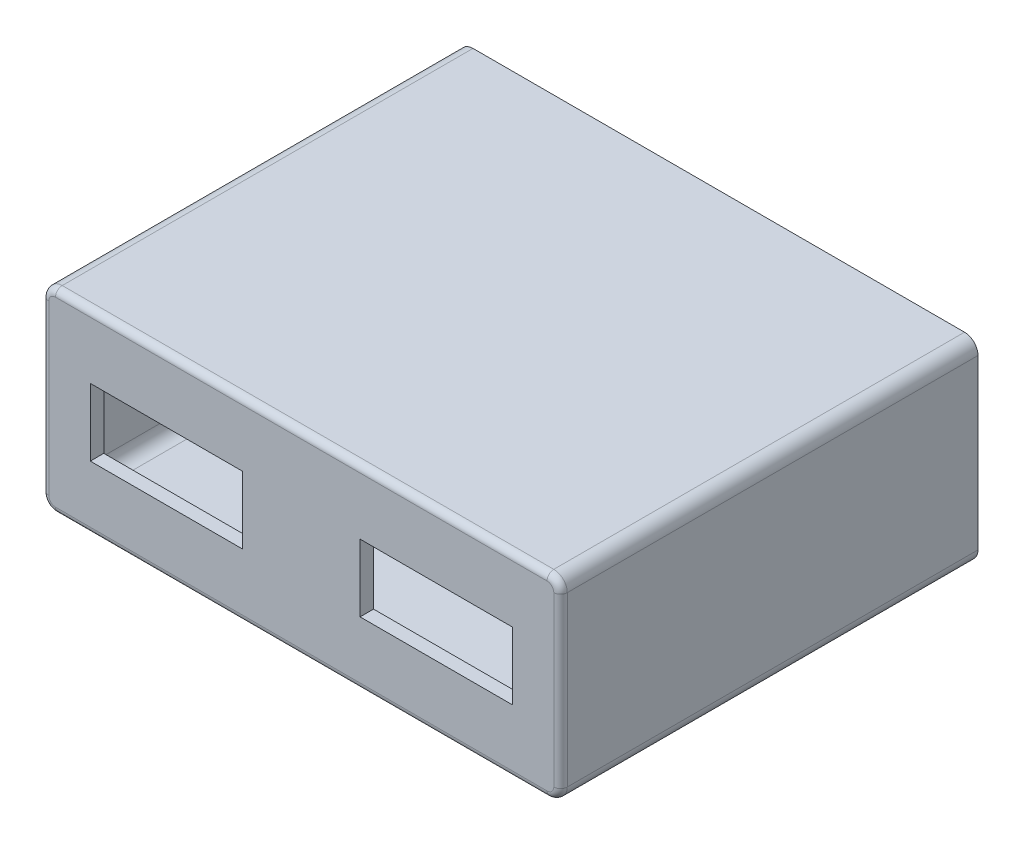
SolidWorks part; units mm, degrees
ref_plane "Front Plane" through (0, 0, 0) normal (0, 0, 1) x (1, 0, 0)
ref_plane "Top Plane" through (0, 0, 0) normal (0, 1, 0) x (1, 0, 0)
ref_plane "Right Plane" through (0, 0, 0) normal (1, 0, 0) x (0, 0, -1)
sketch "Sketch1" plane through (0, 0, 0) normal (0, 0, 1) x (1, 0, 0)
  line L1 (-34.5, -12.5) -> (34.5, -12.5)
  line L2 (-36.5, -10.5) -> (-36.5, 10.5)
  line L3 (-34.5, 12.5) -> (34.5, 12.5)
  line L4 (36.5, -10.5) -> (36.5, 10.5)
  line L5 (-36.5, -12.5) -> (36.5, 12.5) construction
  line L6 (-36.5, 12.5) -> (36.5, -12.5) construction
  line L9 (36.5, -14.5) -> (-36.5, -14.5)
  line L10 (38.5, -12.5) -> (38.5, 12.5)
  line L11 (36.5, 14.5) -> (-36.5, 14.5)
  line L12 (-38.5, -12.5) -> (-38.5, 12.5)
  line L13 (38.5, -14.5) -> (-38.5, 14.5) construction
  line L14 (38.5, 14.5) -> (-38.5, -14.5) construction
  arc A0 (-36.5, -14.5) -> (-38.5, -12.5) centre (-36.5, -12.5) cw
  arc A1 (-36.5, 14.5) -> (-38.5, 12.5) centre (-36.5, 12.5) ccw
  arc A2 (38.5, 12.5) -> (36.5, 14.5) centre (36.5, 12.5) ccw
  arc A3 (36.5, -14.5) -> (38.5, -12.5) centre (36.5, -12.5) ccw
  arc A4 (34.5, -12.5) -> (36.5, -10.5) centre (34.5, -10.5) ccw
  arc A5 (34.5, 12.5) -> (36.5, 10.5) centre (34.5, 10.5) cw
  arc A6 (-34.5, -12.5) -> (-36.5, -10.5) centre (-34.5, -10.5) cw
  arc A7 (-36.5, 10.5) -> (-34.5, 12.5) centre (-34.5, 10.5) cw
  point P0 (0, 0)
  point P10 (0, 0)
  dimension "D1" = 2
extrude "Boss-Extrude1" add sketch "Sketch1" along normal blind 55
sketch "Sketch2" plane through (0, 0, 55) normal (0, 0, 1) x (1, 0, 0)
  line L4 (-36.5, -14.5) -> (36.5, -14.5)
  line L5 (38.5, -12.5) -> (38.5, 12.5)
  line L6 (36.5, 14.5) -> (-36.5, 14.5)
  line L7 (-38.5, 12.5) -> (-38.5, -12.5)
  line L8 (-36.5, -14.5) -> (36.5, -14.5)
  line L9 (38.5, -12.5) -> (38.5, 12.5)
  line L10 (36.5, 14.5) -> (-36.5, 14.5)
  line L11 (-38.5, 12.5) -> (-38.5, -12.5)
  arc A4 (-38.5, -12.5) -> (-36.5, -14.5) centre (-36.5, -12.5) ccw
  arc A5 (36.5, -14.5) -> (38.5, -12.5) centre (36.5, -12.5) ccw
  arc A6 (38.5, 12.5) -> (36.5, 14.5) centre (36.5, 12.5) ccw
  arc A7 (-36.5, 14.5) -> (-38.5, 12.5) centre (-36.5, 12.5) ccw
  arc A8 (-38.5, -12.5) -> (-36.5, -14.5) centre (-36.5, -12.5) ccw
  arc A9 (36.5, -14.5) -> (38.5, -12.5) centre (36.5, -12.5) ccw
  arc A10 (38.5, 12.5) -> (36.5, 14.5) centre (36.5, 12.5) ccw
  arc A11 (-36.5, 14.5) -> (-38.5, 12.5) centre (-36.5, 12.5) ccw
  dimension "D1" = 0
extrude "Boss-Extrude2" add sketch "Sketch2" along normal blind 2
sketch "Sketch3" plane through (0, 0, 57) normal (0, 0, 1) x (1, 0, 0)
  line L1 (-31.3334, 5) -> (-8.7334, 5)
  line L2 (-31.3334, 5) -> (-31.3334, -5)
  line L3 (-31.3334, -5) -> (-8.7334, -5)
  line L4 (-8.7334, 5) -> (-8.7334, -5)
  line L5 (-31.3334, 5) -> (-8.7334, -5) construction
  line L6 (-31.3334, -5) -> (-8.7334, 5) construction
  line L7 (31.3334, -5) -> (8.7334, 5) construction
  line L8 (31.3334, 5) -> (8.7334, -5) construction
  line L9 (8.7334, 5) -> (8.7334, -5)
  line L10 (31.3334, -5) -> (8.7334, -5)
  line L11 (31.3334, 5) -> (31.3334, -5)
  line L12 (31.3334, 5) -> (8.7334, 5)
  point P0 (-20.0334, 0)
  point P12 (20.0334, 0)
extrude "Cut-Extrude1" cut sketch "Sketch3" against normal blind 12
fillet "Fillet1" radius 1 8 edges at (37.9142, 13.9142, 57) (38.5, 0, 57) (37.9142, -13.9142, 57) (0, -14.5, 57) (-37.9142, -13.9142, 57) (-38.5, 0, 57) (-37.9142, 13.9142, 57) (0, 14.5, 57)
sketch "Sketch4" plane through (0, 0, 0) normal (0, 0, -1) x (-1, 0, 0)
  line L4 (38.5, -12.5) -> (38.5, 12.5)
  line L5 (36.5, 14.5) -> (-36.5, 14.5)
  line L6 (-38.5, 12.5) -> (-38.5, -12.5)
  line L7 (-36.5, -14.5) -> (36.5, -14.5)
  line L8 (38.5, -12.5) -> (38.5, 12.5)
  line L9 (36.5, 14.5) -> (-36.5, 14.5)
  line L10 (-38.5, 12.5) -> (-38.5, -12.5)
  line L11 (-36.5, -14.5) -> (36.5, -14.5)
  line L12 (-34.5, -12.5) -> (34.5, -12.5)
  line L13 (36.5, -10.5) -> (36.5, 10.5)
  line L14 (34.5, 12.5) -> (-34.5, 12.5)
  line L15 (-36.5, 10.5) -> (-36.5, -10.5)
  line L16 (-34.5, -12.5) -> (34.5, -12.5)
  line L17 (36.5, -10.5) -> (36.5, 10.5)
  line L18 (34.5, 12.5) -> (-34.5, 12.5)
  line L19 (-36.5, 10.5) -> (-36.5, -10.5)
  arc A4 (36.5, -14.5) -> (38.5, -12.5) centre (36.5, -12.5) ccw
  arc A5 (38.5, 12.5) -> (36.5, 14.5) centre (36.5, 12.5) ccw
  arc A6 (-36.5, 14.5) -> (-38.5, 12.5) centre (-36.5, 12.5) ccw
  arc A7 (-38.5, -12.5) -> (-36.5, -14.5) centre (-36.5, -12.5) ccw
  arc A8 (36.5, -14.5) -> (38.5, -12.5) centre (36.5, -12.5) ccw
  arc A9 (38.5, 12.5) -> (36.5, 14.5) centre (36.5, 12.5) ccw
  arc A10 (-36.5, 14.5) -> (-38.5, 12.5) centre (-36.5, 12.5) ccw
  arc A11 (-38.5, -12.5) -> (-36.5, -14.5) centre (-36.5, -12.5) ccw
  arc A12 (-36.5, -10.5) -> (-34.5, -12.5) centre (-34.5, -10.5) ccw
  arc A13 (34.5, -12.5) -> (36.5, -10.5) centre (34.5, -10.5) ccw
  arc A14 (36.5, 10.5) -> (34.5, 12.5) centre (34.5, 10.5) ccw
  arc A15 (-34.5, 12.5) -> (-36.5, 10.5) centre (-34.5, 10.5) ccw
  arc A16 (-36.5, -10.5) -> (-34.5, -12.5) centre (-34.5, -10.5) ccw
  arc A17 (34.5, -12.5) -> (36.5, -10.5) centre (34.5, -10.5) ccw
  arc A18 (36.5, 10.5) -> (34.5, 12.5) centre (34.5, 10.5) ccw
  arc A19 (-34.5, 12.5) -> (-36.5, 10.5) centre (-34.5, 10.5) ccw
  dimension "D1" = 0
  dimension "D2" = 0
extrude "Boss-Extrude3" add sketch "Sketch4" along normal blind 5
